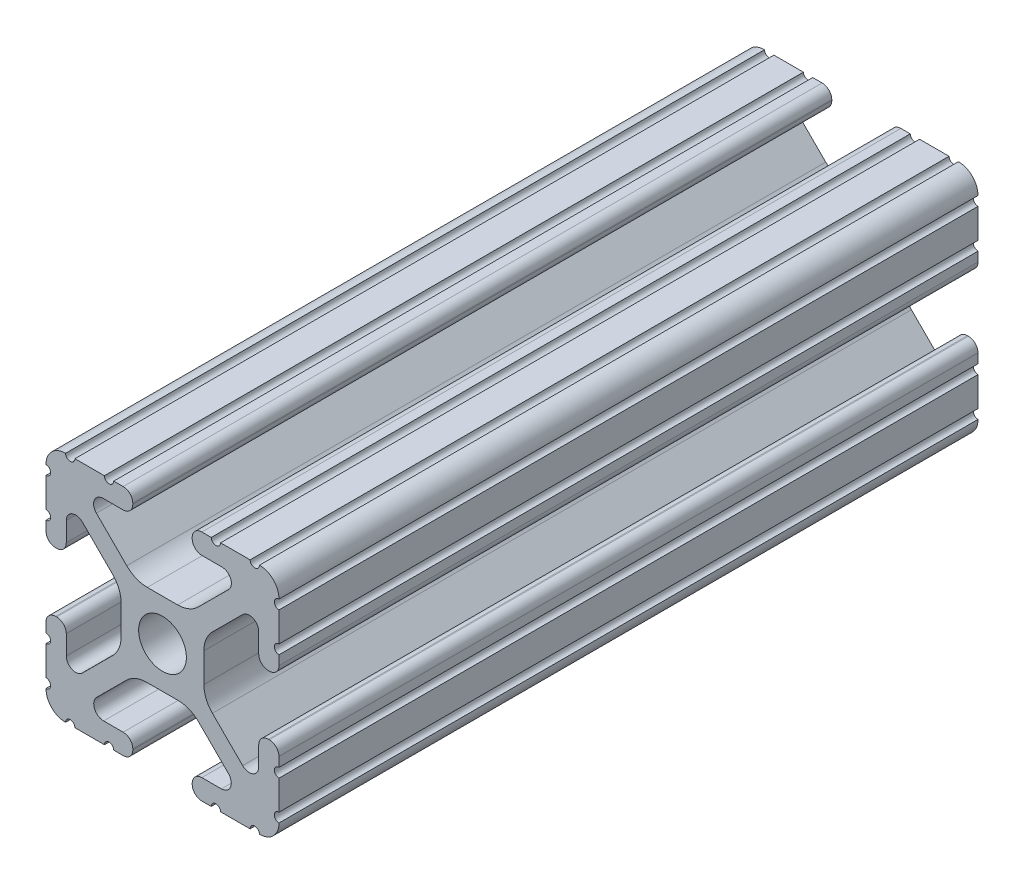
SolidWorks part; units mm, degrees
ref_plane "Front Plane" through (0, 0, 0) normal (0, 0, 1) x (1, 0, 0)
ref_plane "Top Plane" through (0, 0, 0) normal (0, 1, 0) x (1, 0, 0)
ref_plane "Right Plane" through (0, 0, 0) normal (1, 0, 0) x (0, 0, -1)
sketch "Sketch1" plane through (0, 0, 0) normal (0, 0, 1) x (1, 0, 0)
  line L88 (-7.1797, -8.6452) -> (-3.9523, -5.4237)
  line L89 (-1.7093, -4.4958) -> (1.7093, -4.4958)
  line L90 (3.9523, -5.4237) -> (7.1797, -8.6452)
  line L91 (6.4164, -10.4902) -> (4.2875, -10.4902)
  line L92 (3.2385, -11.5392) -> (3.2385, -11.651)
  line L93 (4.2875, -12.7) -> (5.3171, -12.7)
  line L94 (6.3331, -12.7) -> (9.5504, -12.7)
  line L95 (12.7, -9.5504) -> (12.7, -6.3331)
  line L96 (12.7, -5.3171) -> (12.7, -4.2875)
  line L97 (11.651, -3.2385) -> (11.5392, -3.2385)
  line L98 (10.4902, -4.2875) -> (10.4902, -6.4021)
  line L99 (8.7371, -7.1294) -> (5.441, -3.8408)
  line L100 (4.5085, -1.5932) -> (4.5085, 1.5932)
  line L101 (5.441, 3.8408) -> (8.7371, 7.1294)
  line L102 (10.4902, 6.4021) -> (10.4902, 4.2875)
  line L103 (11.5392, 3.2385) -> (11.651, 3.2385)
  line L104 (12.7, 4.2875) -> (12.7, 5.3171)
  line L105 (12.7, 6.3331) -> (12.7, 9.5504)
  line L106 (9.5504, 12.7) -> (6.3331, 12.7)
  line L107 (5.3171, 12.7) -> (4.2875, 12.7)
  line L108 (3.2385, 11.651) -> (3.2385, 11.5392)
  line L109 (4.2875, 10.4902) -> (6.4768, 10.4902)
  line L110 (7.207, 8.7244) -> (3.8983, 5.4232)
  line L111 (1.6558, 4.4958) -> (-1.6558, 4.4958)
  line L112 (-3.8983, 5.4232) -> (-7.207, 8.7244)
  line L113 (-6.4768, 10.4902) -> (-4.2875, 10.4902)
  line L114 (-3.2385, 11.5392) -> (-3.2385, 11.651)
  line L115 (-4.2875, 12.7) -> (-5.3171, 12.7)
  line L116 (-6.3331, 12.7) -> (-9.5504, 12.7)
  line L117 (-12.7, 9.5504) -> (-12.7, 6.3331)
  line L118 (-12.7, 5.3171) -> (-12.7, 4.2875)
  line L119 (-11.651, 3.2385) -> (-11.5392, 3.2385)
  line L120 (-10.4902, 4.2875) -> (-10.4902, 6.4021)
  line L121 (-8.7371, 7.1294) -> (-5.441, 3.8408)
  line L122 (-4.5085, 1.5932) -> (-4.5085, -1.5932)
  line L123 (-5.441, -3.8408) -> (-8.7371, -7.1294)
  line L124 (-10.4902, -6.4021) -> (-10.4902, -4.2875)
  line L125 (-11.5392, -3.2385) -> (-11.651, -3.2385)
  line L126 (-12.7, -4.2875) -> (-12.7, -5.3171)
  line L127 (-12.7, -6.3331) -> (-12.7, -9.5504)
  line L128 (-9.5504, -12.7) -> (-6.3331, -12.7)
  line L129 (-5.3171, -12.7) -> (-4.2875, -12.7)
  line L130 (-3.2385, -11.651) -> (-3.2385, -11.5392)
  line L131 (-4.2875, -10.4902) -> (-6.4164, -10.4902)
  circle A1 centre (0, 0) radius 2.6035
  arc A104 (-7.1797, -8.6452) -> (-6.4164, -10.4902) centre (-6.4164, -9.4098) ccw
  arc A105 (-1.7093, -4.4958) -> (-3.9523, -5.4237) centre (-1.7093, -7.6708) ccw
  arc A106 (3.9523, -5.4237) -> (1.7093, -4.4958) centre (1.7093, -7.6708) ccw
  arc A107 (6.4164, -10.4902) -> (7.1797, -8.6452) centre (6.4164, -9.4098) ccw
  arc A108 (4.2875, -10.4902) -> (3.2385, -11.5392) centre (4.2875, -11.5392) ccw
  arc A109 (3.2385, -11.651) -> (4.2875, -12.7) centre (4.2875, -11.651) ccw
  arc A110 (6.3331, -12.7) -> (5.3171, -12.7) centre (5.8251, -12.7) ccw
  arc A111 (10.5664, -12.6998) -> (9.5504, -12.7) centre (10.0584, -12.7) ccw
  arc A112 (10.5664, -12.6998) -> (12.6998, -10.5664) centre (10.5918, -10.5918) ccw
  arc A113 (12.7, -9.5504) -> (12.6998, -10.5664) centre (12.7, -10.0584) ccw
  arc A114 (12.7, -5.3171) -> (12.7, -6.3331) centre (12.7, -5.8251) ccw
  arc A115 (12.7, -4.2875) -> (11.651, -3.2385) centre (11.651, -4.2875) ccw
  arc A116 (11.5392, -3.2385) -> (10.4902, -4.2875) centre (11.5392, -4.2875) ccw
  arc A117 (8.7371, -7.1294) -> (10.4902, -6.4021) centre (9.4628, -6.4021) ccw
  arc A118 (4.5085, -1.5932) -> (5.441, -3.8408) centre (7.6835, -1.5932) ccw
  arc A119 (5.441, 3.8408) -> (4.5085, 1.5932) centre (7.6835, 1.5932) ccw
  arc A120 (10.4902, 6.4021) -> (8.7371, 7.1294) centre (9.4628, 6.4021) ccw
  arc A121 (10.4902, 4.2875) -> (11.5392, 3.2385) centre (11.5392, 4.2875) ccw
  arc A122 (11.651, 3.2385) -> (12.7, 4.2875) centre (11.651, 4.2875) ccw
  arc A123 (12.7, 6.3331) -> (12.7, 5.3171) centre (12.7, 5.8251) ccw
  arc A124 (12.6998, 10.5664) -> (12.7, 9.5504) centre (12.7, 10.0584) ccw
  arc A125 (12.6998, 10.5664) -> (10.5664, 12.6998) centre (10.5918, 10.5918) ccw
  arc A126 (9.5504, 12.7) -> (10.5664, 12.6998) centre (10.0584, 12.7) ccw
  arc A127 (5.3171, 12.7) -> (6.3331, 12.7) centre (5.8251, 12.7) ccw
  arc A128 (4.2875, 12.7) -> (3.2385, 11.651) centre (4.2875, 11.651) ccw
  arc A129 (3.2385, 11.5392) -> (4.2875, 10.4902) centre (4.2875, 11.5392) ccw
  arc A130 (7.207, 8.7244) -> (6.4768, 10.4902) centre (6.4768, 9.4563) ccw
  arc A131 (1.6558, 4.4958) -> (3.8983, 5.4232) centre (1.6558, 7.6708) ccw
  arc A132 (-3.8983, 5.4232) -> (-1.6558, 4.4958) centre (-1.6558, 7.6708) ccw
  arc A133 (-6.4768, 10.4902) -> (-7.207, 8.7244) centre (-6.4768, 9.4563) ccw
  arc A134 (-4.2875, 10.4902) -> (-3.2385, 11.5392) centre (-4.2875, 11.5392) ccw
  arc A135 (-3.2385, 11.651) -> (-4.2875, 12.7) centre (-4.2875, 11.651) ccw
  arc A136 (-6.3331, 12.7) -> (-5.3171, 12.7) centre (-5.8251, 12.7) ccw
  arc A137 (-10.5664, 12.6998) -> (-9.5504, 12.7) centre (-10.0584, 12.7) ccw
  arc A138 (-10.5664, 12.6998) -> (-12.6998, 10.5664) centre (-10.5918, 10.5918) ccw
  arc A139 (-12.7, 9.5504) -> (-12.6998, 10.5664) centre (-12.7, 10.0584) ccw
  arc A140 (-12.7, 5.3171) -> (-12.7, 6.3331) centre (-12.7, 5.8251) ccw
  arc A141 (-12.7, 4.2875) -> (-11.651, 3.2385) centre (-11.651, 4.2875) ccw
  arc A142 (-11.5392, 3.2385) -> (-10.4902, 4.2875) centre (-11.5392, 4.2875) ccw
  arc A143 (-8.7371, 7.1294) -> (-10.4902, 6.4021) centre (-9.4628, 6.4021) ccw
  arc A144 (-4.5085, 1.5932) -> (-5.441, 3.8408) centre (-7.6835, 1.5932) ccw
  arc A145 (-5.441, -3.8408) -> (-4.5085, -1.5932) centre (-7.6835, -1.5932) ccw
  arc A146 (-10.4902, -6.4021) -> (-8.7371, -7.1294) centre (-9.4628, -6.4021) ccw
  arc A147 (-10.4902, -4.2875) -> (-11.5392, -3.2385) centre (-11.5392, -4.2875) ccw
  arc A148 (-11.651, -3.2385) -> (-12.7, -4.2875) centre (-11.651, -4.2875) ccw
  arc A149 (-12.7, -6.3331) -> (-12.7, -5.3171) centre (-12.7, -5.8251) ccw
  arc A150 (-12.6998, -10.5664) -> (-12.7, -9.5504) centre (-12.7, -10.0584) ccw
  arc A151 (-12.6998, -10.5664) -> (-10.5664, -12.6998) centre (-10.5918, -10.5918) ccw
  arc A152 (-9.5504, -12.7) -> (-10.5664, -12.6998) centre (-10.0584, -12.7) ccw
  arc A153 (-5.3171, -12.7) -> (-6.3331, -12.7) centre (-5.8251, -12.7) ccw
  arc A154 (-4.2875, -12.7) -> (-3.2385, -11.651) centre (-4.2875, -11.651) ccw
  arc A155 (-3.2385, -11.5392) -> (-4.2875, -10.4902) centre (-4.2875, -11.5392) ccw
extrude "Boss-Extrude1" add sketch "Sketch1" along normal mid plane 76.2
